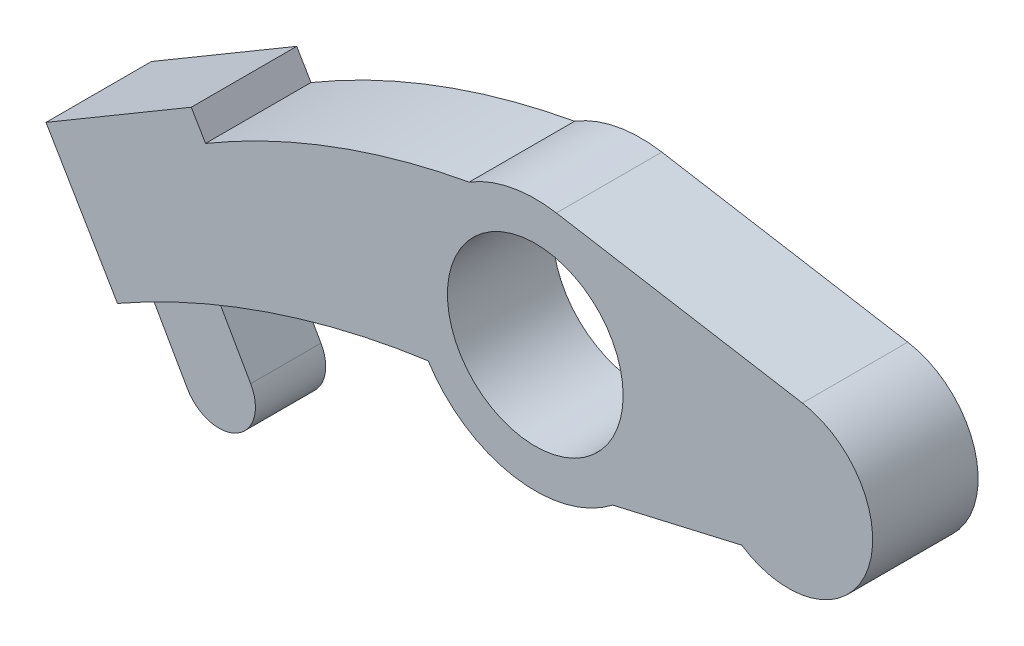
SolidWorks part; units mm, degrees
ref_plane "Front Plane" through (0, 0, 0) normal (0, 0, 1) x (1, 0, 0)
ref_plane "Top Plane" through (0, 0, 0) normal (0, 1, 0) x (1, 0, 0)
ref_plane "Right Plane" through (0, 0, 0) normal (1, 0, 0) x (0, 0, -1)
sketch "Sketch1" plane through (0, 0, 0) normal (0, 0, 1) x (1, 0, 0)
  line L0 (19, 5.9161) -> (1.2088, 8.9233)
  line L1 (14.6834, -5) -> (5.5069, -7.1185)
  line L2 (-23.454, 0.6815) -> (-24.4708, 2.4037)
  line L3 (-24.4708, 2.4037) -> (-34.8042, -3.6973)
  line L4 (-34.8042, -3.6973) -> (-29.72, -12.3084)
  line L6 (0, 20.4267) -> (0, -20.4267) construction
  circle A0 centre (0, 0) radius 6.25
  arc A1 (1.5, 8.8741) -> (-4.7045, 7.6725) centre (0, 0) ccw
  arc A2 (14.6834, -5) -> (19, 5.9161) centre (18, 0) ccw
  arc A3 (-4.7045, 7.6725) -> (-23.454, 0.6815) centre (5.5257, -48.4019) ccw
  arc A4 (-29.72, -12.3084) -> (-7.6175, -4.793) centre (0.9336, -66.2005) cw
  arc A5 (-7.6175, -4.793) -> (5.5069, -7.1185) centre (0, 0) ccw
  point P12 (0, 0)
  point P20 (0, 0)
  point P21 (0, 0)
  point P24 (0, 0)
  point P25 (0, 0)
  point P26 (0, 0)
  point P27 (0, 0)
  point P28 (0, 0)
  point P29 (0, 0)
  point P30 (-7.6175, -5)
  dimension "D1" = 18
  dimension "D2" = 12.5
  dimension "D3" = 12
  dimension "D5" = 2
  dimension "D10" = 29.72
  dimension "D6" = 57
  dimension "D11" = 62
  dimension "D4" = 5
  dimension "D7" = 12
  dimension "D8" = 35
  dimension "D9" = 10
extrude "Boss-Extrude1" add sketch "Sketch1" along normal mid plane 7.5 contours L6 A1 A3 L2 L3 L4 A4 A5 A0 | A1 L6 A0 A5 L1 A2 L0
sketch "Sketch2" plane through (0, 0, 0) normal (0, 0, 1) x (1, 0, 0)
  line L0 (-28.6335, -11.6904) -> (-24.1318, -9.1299)
  line L1 (-28.6335, -11.6904) -> (-25.9963, -16.3269)
  line L2 (-24.1318, -9.1299) -> (-23.9687, -9.4213)
  line L3 (-21.4966, -13.7675) -> (-23.9687, -9.4213)
  arc A0 (-7.6175, -4.793) -> (-29.72, -12.3084) centre (0.9336, -66.2005) ccw construction
  arc A1 (-25.9963, -16.3269) -> (-21.4966, -13.7675) centre (-23.7464, -15.0472) ccw
  dimension "D2" = 5
extrude "Boss-Extrude2" add sketch "Sketch2" along normal mid plane 5
